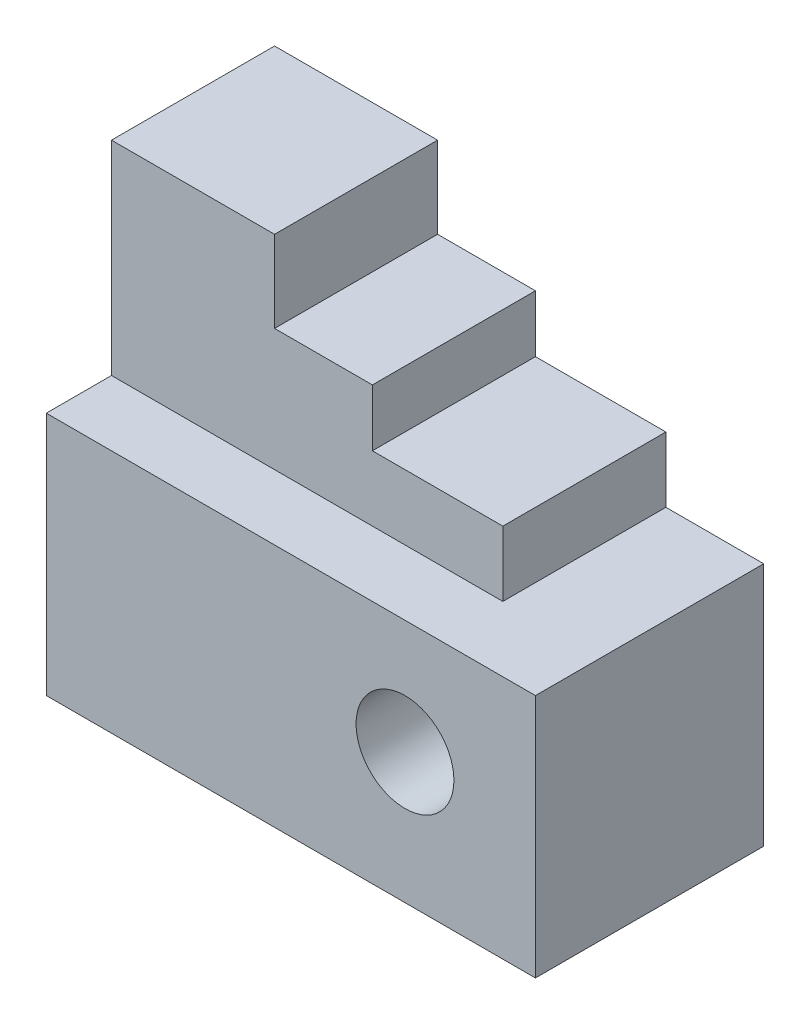
SolidWorks part; units mm, degrees
ref_plane "Front Plane" through (0, 0, 0) normal (0, 0, 1) x (1, 0, 0)
ref_plane "Top Plane" through (0, 0, 0) normal (0, 1, 0) x (1, 0, 0)
ref_plane "Right Plane" through (0, 0, 0) normal (1, 0, 0) x (0, 0, -1)
sketch "Sketch1" plane through (0, 0, 0) normal (0, 0, 1) x (1, 0, 0)
  line L0 (0, 0) -> (60, 0)
  line L1 (0, 0) -> (0, 30)
  line L2 (0, 30) -> (60, 30)
  line L3 (60, 30) -> (60, 0)
  dimension "D1" = 60
  dimension "D2" = 30
extrude "Boss-Extrude1" add sketch "Sketch1" along normal blind 28
sketch "Sketch2" plane through (0, 0, 28) normal (0, 0, 1) x (1, 0, 0)
  line L0 (60, 0) -> (44, 0)
  line L1 (0, 0) -> (60, 0) construction
  line L2 (60, 0) -> (60, 16)
  line L3 (60, 0) -> (60, 30) construction
  circle A0 centre (44, 16) radius 6
  dimension "D1" = 16
  dimension "D2" = 16
extrude "Cut-Extrude1" cut sketch "Sketch2" against normal blind 28 contours A0
sketch "Sketch3" plane through (0, 30, 0) normal (0, 1, 0) x (1, 0, 0)
  line L0 (60, 0) -> (48, 0)
  line L1 (60, 0) -> (0, 0) construction
  line L2 (48, 0) -> (48, -20)
  line L3 (48, -20) -> (0, -20)
  line L4 (0, -28) -> (0, 0) construction
  line L5 (0, 0) -> (20, 0)
  line L6 (20, 0) -> (20, -20)
  line L7 (20, 0) -> (32, 0)
  line L8 (32, 0) -> (32, -20)
  line L9 (32, 0) -> (48, 0)
  line M5 (60, 0) -> (0, 0)
  line M6 (0, 0) -> (0, -28)
  dimension "D1" = 12
  dimension "D2" = 20
  dimension "D3" = 12
extrude "Boss-Extrude3" add sketch "Sketch3" along normal blind 25 contours L6 L3 M5 M6
sketch "Sketch5" plane through (0, 30, 0) normal (0, 1, 0) x (1, 0, 0)
  line L0 (20, -20) -> (20, 0)
  line L1 (60, 0) -> (20, 0) construction
  line L3 (20, -20) -> (32, -20)
  line L4 (20, 0) -> (32, 0)
  line L5 (32, 0) -> (32, -20)
  dimension "D1" = 12
extrude "Boss-Extrude4" add sketch "Sketch5" along normal blind 15
sketch "Sketch6" plane through (0, 30, 0) normal (0, 1, 0) x (1, 0, 0)
  line L1 (60, 0) -> (32, 0) construction
  line L3 (32, -20) -> (48, -20)
  line L4 (48, 0) -> (48, -20)
sketch "Sketch8" plane through (0, 30, 0) normal (0, 1, 0) x (1, 0, 0)
  line L0 (32, 0) -> (48, 0)
  line L1 (32, -20) -> (48, -20)
  line L2 (48, -20) -> (48, 0)
  line L3 (32, -20) -> (32, 0)
extrude "Boss-Extrude5" add sketch "Sketch8" along normal blind 8
